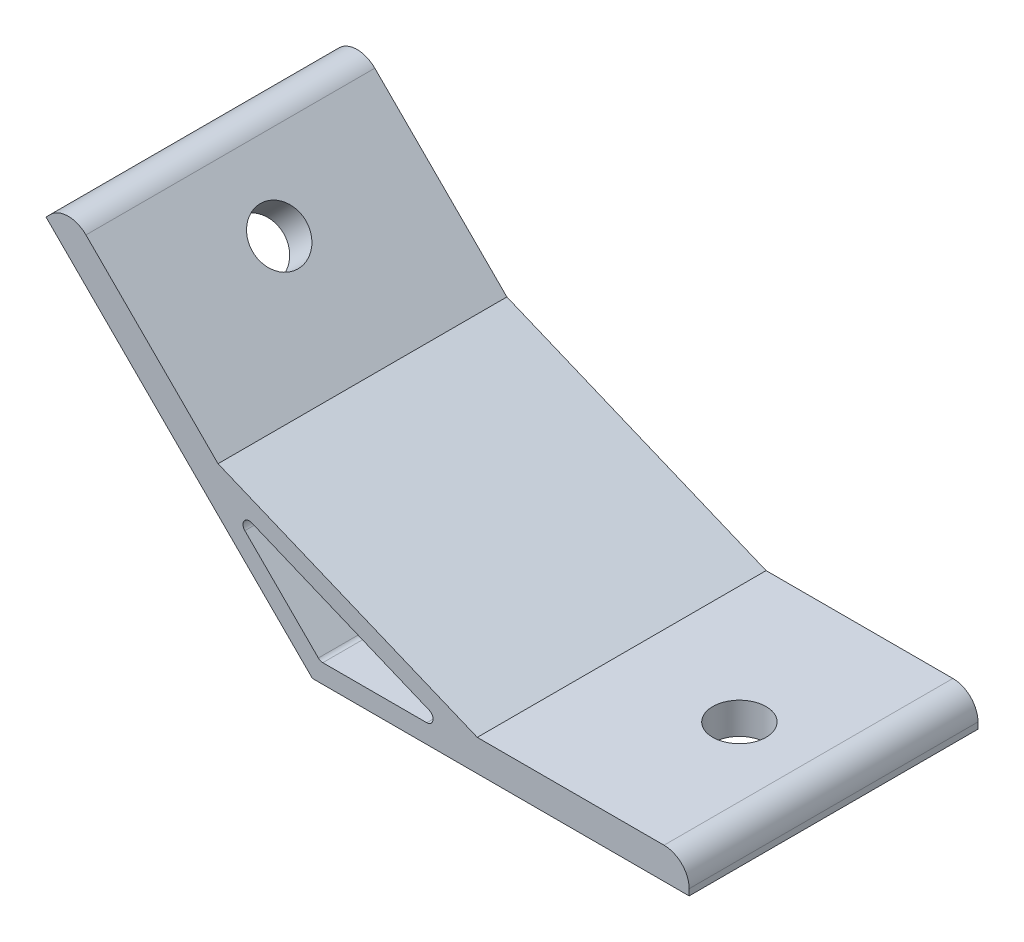
SolidWorks part; units mm, degrees
material "6063 T5"
ref_plane "Спереди" through (0, 0, 0) normal (0, 0, 1) x (1, 0, 0)
ref_plane "Сверху" through (0, 0, 0) normal (0, 1, 0) x (1, 0, 0)
ref_plane "Справа" through (0, 0, 0) normal (1, 0, 0) x (0, 0, -1)
sketch "Эскиз1" plane through (0, 0, 0) normal (0, 0, 1) x (1, 0, 0)
  line L0 (0, 0) -> (-42.4264, 42.4264)
  line L1 (-42.4264, 42.4264) -> (-38.8909, 45.9619)
  line L2 (-38.8909, 45.9619) -> (-15.0286, 22.0996)
  line L3 (-15.0286, 22.0996) -> (26.2536, 5)
  line L4 (26.2536, 5) -> (60, 5)
  line L5 (60, 5) -> (60, 0)
  line L6 (60, 0) -> (0, 0)
  line L7 (-14.3137, 18.5563) -> (23.2426, 3)
  line L8 (23.2426, 3) -> (1.2426, 3)
  line L9 (1.2426, 3) -> (-14.3137, 18.5563)
  line L10 (12.2426, 3) -> (12.2426, 0) construction
  line L11 (-6.5355, 10.7782) -> (-8.6569, 8.6569) construction
  line L12 (0, 0) -> (4.4645, 10.7782) construction
  dimension "D1" = 60
  dimension "D2" = 135
  dimension "D3" = 3
  dimension "D4" = 5
  dimension "D5" = 3
  dimension "D6" = 22
extrude "Бобышка-Вытянуть1" add sketch "Эскиз1" along normal mid plane 46
sketch "Эскиз2" plane through (0, 0, 0) normal (-0.7071, -0.7071, 0) x (0, 0, 1)
  line L0 (23, 60) -> (-23, 60) construction
  circle A0 centre (0, 45) radius 4.25
  dimension "D1" = 8.5
  dimension "D2" = 15
extrude "Вырез-Вытянуть1" cut sketch "Эскиз2" against normal up to surface (5 mm away) up to face at (-26.9597, 34.0308, 0)
sketch "Эскиз3" plane through (0, 0, 0) normal (0, -1, 0) x (1, 0, 0)
  line L0 (60, 23) -> (60, -23) construction
  circle A0 centre (45, 0) radius 4.25
  dimension "D1" = 8.5
  dimension "D2" = 15
extrude "Вырез-Вытянуть2" cut sketch "Эскиз3" against normal up to surface (5 mm away) up to face at (43.1268, 5, 0)
fillet "Скругление1" radius 4 2 edges at (60, 5, 0) (-38.8909, 45.9619, 0)
fillet "Скругление2" radius 1 3 edges at (-14.3137, 18.5563, 0) (1.2426, 3, 0) (23.2426, 3, 0)
